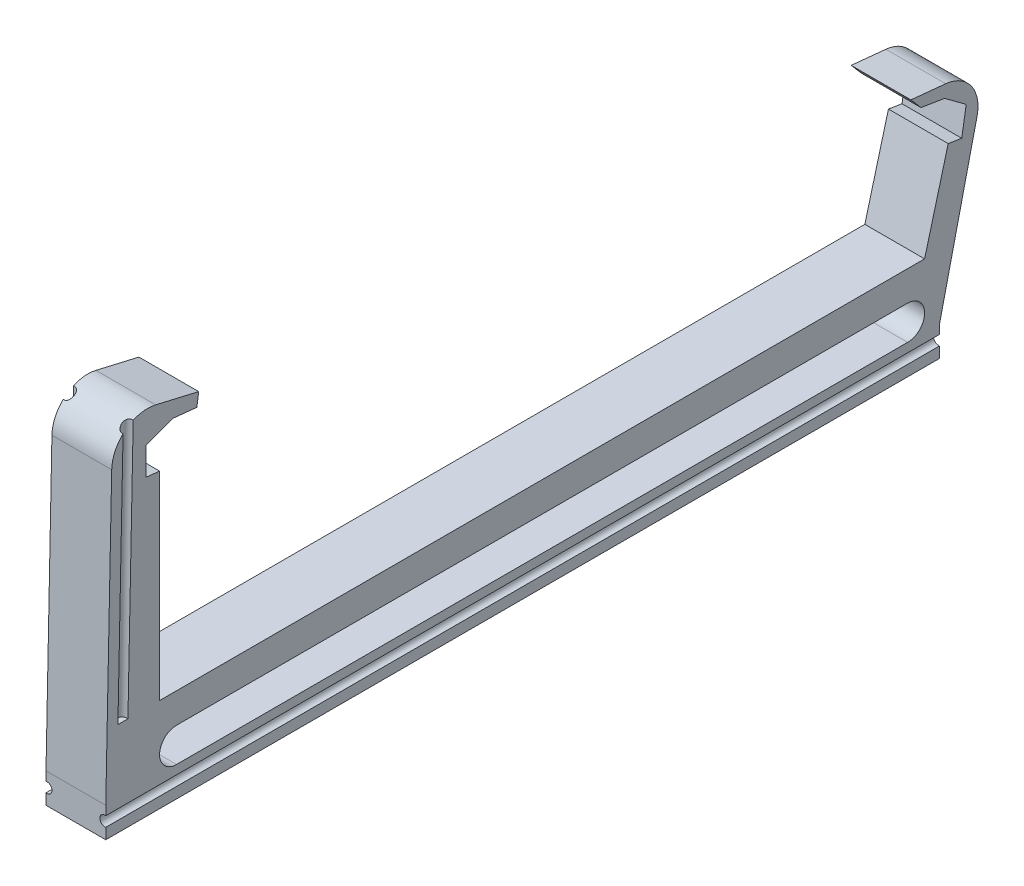
SolidWorks part; units mm, degrees
ref_plane "Front Plane" through (0, 0, 0) normal (0, 0, 1) x (1, 0, 0)
ref_plane "Top Plane" through (0, 0, 0) normal (0, 1, 0) x (1, 0, 0)
ref_plane "Right Plane" through (0, 0, 0) normal (1, 0, 0) x (0, 0, -1)
sketch "Sketch1" plane through (0, 0, 0) normal (1, 0, 0) x (0, 0, -1)
  line L0 (0, 40) -> (0, 0) construction
  line L1 (0, 0) -> (128, 0)
  line L2 (128, 0) -> (133.6811, 21.2021) construction
  line L3 (0, 40) -> (6.2429, 39.3659) construction
  line L4 (133.6811, 21.2021) -> (127.393, 22.2205) construction
  line L5 (6.2429, 39.3659) -> (6.5483, 41.4935)
  line L6 (6.5483, 41.4935) -> (-0.649, 43.1697)
  line L7 (-8.0086, 37.4497) -> (-9, -10.68)
  line L8 (-9, -10.68) -> (130.5, -10.68) construction
  line L9 (130.5, -10.68) -> (136.778, 16.2769)
  line L10 (131.521, 23.6091) -> (125.7106, 24.1798)
  line L11 (125.7106, 24.1798) -> (127.393, 22.2205)
  line L12 (0, 0) -> (0, -10.68) construction
  line L13 (2.84, -7.84) -> (125.16, -7.84) construction
  line L14 (2.84, -5) -> (125.16, -5)
  line L15 (2.84, -10.68) -> (125.16, -10.68)
  line L16 (-9, -10.68) -> (-9, -15.68)
  line L17 (-9, -15.68) -> (130.5, -15.68)
  line L18 (130.5, -15.68) -> (130.5, -10.68)
  line L19 (6.2429, 39.3659) -> (2.2634, 39.7701)
  line L20 (0, 33.25) -> (-2.2882, 33.4824)
  line L21 (-2.2882, 33.4824) -> (-2.2882, 38.0824)
  line L22 (-2.2882, 38.0824) -> (2.2634, 39.7701)
  line L23 (0, 33.25) -> (0, 40) construction
  line L24 (0, 33.25) -> (0, 0)
  line L25 (128, 0) -> (131.947, 14.7304)
  line L26 (131.947, 14.7304) -> (134.2174, 14.3626)
  line L27 (134.2174, 14.3626) -> (134.9529, 18.9035)
  line L28 (134.9529, 18.9035) -> (131.3416, 21.581)
  line L29 (131.3416, 21.581) -> (127.393, 22.2205)
  arc A0 (2.84, -5) -> (2.84, -10.68) centre (2.84, -7.84) ccw
  arc A1 (125.16, -10.68) -> (125.16, -5) centre (125.16, -7.84) ccw
  arc A2 (136.778, 16.2769) -> (131.521, 23.6091) centre (130.9344, 17.6378) ccw
  arc A3 (-0.649, 43.1697) -> (-8.0086, 37.4497) centre (-2.0099, 37.3261) ccw
  point P3 (64, -7.84)
  point P22 (64, 0)
  point P26 (138.3299, 22.9403)
  point P29 (-7.8562, 44.8482)
  dimension "D22" = 6
  dimension "D1" = 40
  dimension "D2" = 128
  dimension "D3" = 21.95
  dimension "D4" = 105
  dimension "D5" = 84.2
  dimension "D6" = 6.37
  dimension "D7" = 84.2
  dimension "D8" = 6.275
  dimension "D9" = 139.5
  dimension "D10" = 55.54
  dimension "D11" = 34.52
  dimension "D12" = 10.68
  dimension "D13" = 103.11
  dimension "D14" = 88.82
  dimension "D15" = 9
  dimension "D16" = 12.68
  dimension "D17" = 82.5
  dimension "D18" = 14.79
  dimension "D19" = 78.07
  dimension "D20" = 5
  dimension "D21" = 5
  dimension "D23" = 2.3
  dimension "D24" = 4.6
  dimension "D25" = 4
  dimension "D26" = 33.25
  dimension "D27" = 2.3
  dimension "D28" = 4.6
  dimension "D29" = 4
  dimension "D30" = 15.25
  dimension "D31" = 95.8
  dimension "D32" = 95.8
extrude "Boss-Extrude1" add sketch "Sketch1" along normal blind 10
ref_plane "Plane1" through (0, 43.2676, -0.8912) normal (0, 0.9998, -0.0206) x (1, 0, 0)
sketch "Sketch2" plane through (0, 43.2676, -0.8912) normal (0, 0.9998, -0.0206) x (1, 0, 0)
  line L0 (0, -8.7782) -> (10, -8.7782)
  line L1 (10, -8.7782) -> (10, 5.6924)
  line L2 (10, 5.6924) -> (0, 5.6924)
  line L3 (0, 5.6924) -> (0, -8.7782)
  line L4 (5, -8.7782) -> (5, 5.6924) construction
  arc A0 (0, -6.9648) -> (0, -5.2915) centre (0.15, -6.1282) ccw
  arc A1 (10, -6.9648) -> (10, -5.2915) centre (9.85, -6.1282) cw
  dimension "D2" = 0.85
  dimension "D1" = 0.15
  dimension "D3" = 2.65
ref_plane "Plane2" through (0, 0, 0) normal (0, 1, 0) x (1, 0, 0)
extrude "Cut-Extrude4" cut sketch "Sketch2" against normal up to surface (43.4202 mm away) contours L3 A0 up to plane "Plane2"
ref_plane "Plane3" through (5, 0, 0) normal (1, 0, 0) x (0, 0, -1)
mirror "Mirror1" about plane through (5, 0, 0) normal (1, 0, 0) of "Cut-Extrude4"
sketch "Sketch3" plane through (0, 0, 0) normal (0, 0, 1) x (1, 0, 0)
  line L0 (0, -10.68) -> (0, -15.68)
  line L1 (0, -15.68) -> (0, -10.68) construction
  line L2 (0, -15.68) -> (10, -15.68)
  line L3 (10, -15.68) -> (10, -10.68)
  line L4 (10, -10.68) -> (0, -10.68)
  arc A0 (0, -13.8667) -> (0, -12.1933) centre (0.15, -13.03) ccw
  dimension "D2" = 0.85
  dimension "D1" = 0.15
  dimension "D3" = 2.65
extrude "Cut-Extrude5" cut sketch "Sketch3" against normal through all and the other way through all contours A0
mirror "Mirror2" about plane through (5, 0, 0) normal (1, 0, 0) of "Cut-Extrude5"
